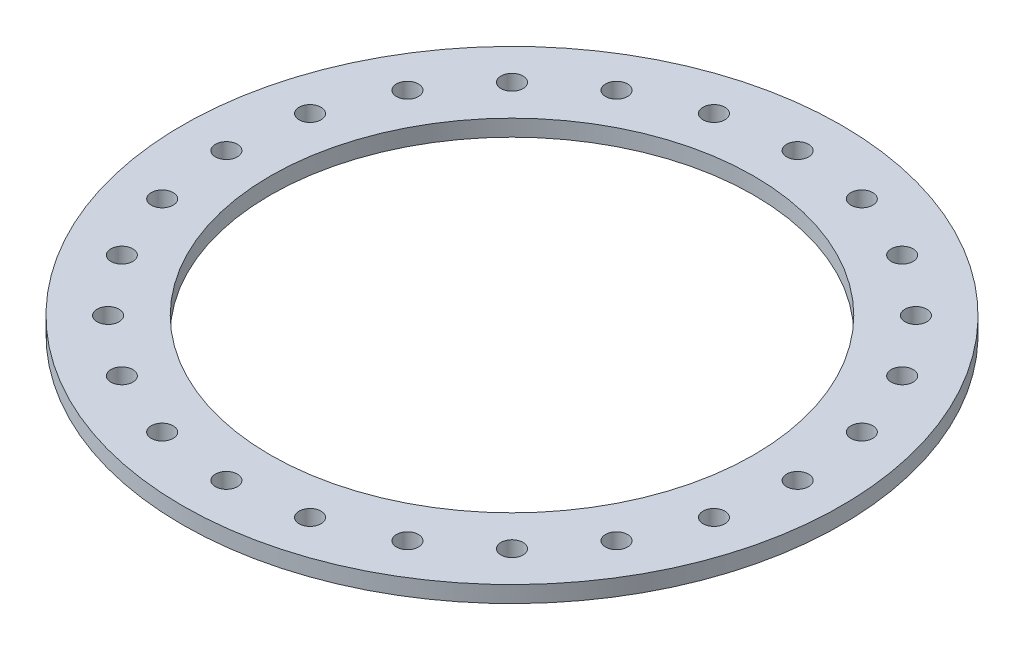
SolidWorks part; units mm, degrees
material "Pine"
ref_plane "Front Plane" through (0, 0, 0) normal (0, 0, 1) x (1, 0, 0)
ref_plane "Top Plane" through (0, 0, 0) normal (0, 1, 0) x (1, 0, 0)
ref_plane "Right Plane" through (0, 0, 0) normal (1, 0, 0) x (0, 0, -1)
sketch "Sketch1" plane through (0, 0, 0) normal (0, 1, 0) x (1, 0, 0)
  circle A0 centre (0, 0) radius 381
  circle A1 centre (0, 0) radius 279.4
  dimension "D1" = 762
  dimension "D2" = 101.6
extrude "Boss-Extrude1" add sketch "Sketch1" along normal blind 19.05
hole_wizard "1 (1) Diameter Hole1" positions "Sketch3" profile "Sketch2" hole size "1" standard "ANSI Inch"
sketch "Sketch3" plane through (0, 19.05, 0) normal (0, 1, 0) x (1, 0, 0)
  line L0 (0, 0) -> (0, 495.6028) construction
  point P0 (0, 330.2)
  dimension "D1" = 330.2
  dimension "D4" = 0
sketch "Sketch2" plane through (0, 19.05, -330.2) normal (1, 0, 0) x (0, 0, 1)
  line L0 (0, 0) -> (0, 39.6309)
  line L1 (0, 39.6309) -> (12.7, 32)
  line L2 (12.7, 32) -> (12.7, 0)
  line L5 (12.7, 0) -> (0, 0)
  line L10 (0, 39.6309) -> (-12.7, 32) construction
  line L11 (0, -6.35) -> (0, 107.95) construction
  dimension "Hole Dia." = 25.4
  dimension "Hole Depth" = 32
  dimension "Drill Angle" = 118
pattern_circular "CirPattern1" count 24 over 360 about axis through (0, 0, 0) along (0, 1, 0) of "1 (1) Diameter Hole1"
